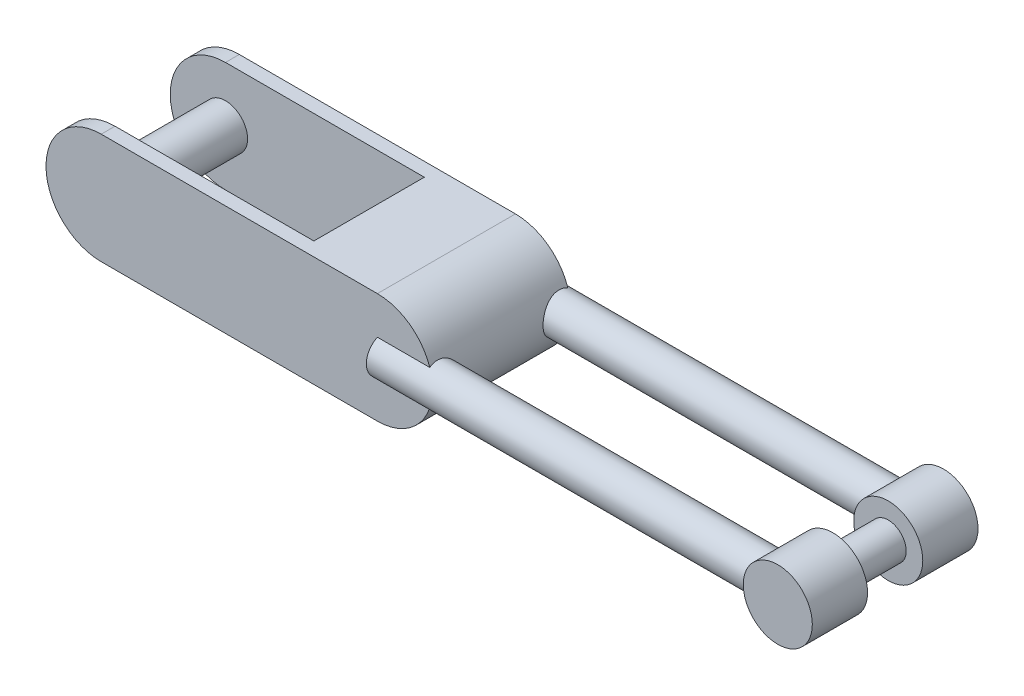
SolidWorks part; units mm, degrees
material "Brass"
ref_plane "Front Plane" through (0, 0, 0) normal (0, 0, 1) x (1, 0, 0)
ref_plane "Top Plane" through (0, 0, 0) normal (0, 1, 0) x (1, 0, 0)
ref_plane "Right Plane" through (0, 0, 0) normal (1, 0, 0) x (0, 0, -1)
other "Configuration Table"
sketch "Sketch1" plane through (0, 0, 0) normal (0, 0, 1) x (1, 0, 0)
  line L0 (0, 10) -> (50, 10)
  line L1 (0, -10) -> (50, -10)
  circle A0 centre (0, 0) radius 10
  circle A1 centre (50, 0) radius 10
  dimension "D1" = 20
  dimension "D2" = 20
  dimension "D3" = 50
extrude "Extrude1" add sketch "Sketch1" against normal mid plane 25
sketch "Sketch2" plane through (0, 10, 0) normal (0, 1, 0) x (-1, 0, 0)
  line L1 (-36, 10) -> (14, 10)
  line L2 (-36, 10) -> (-36, -10)
  line L3 (-36, -10) -> (14, -10)
  line L4 (14, 10) -> (14, -10)
  line L5 (-50, 0) -> (-36, 0) construction
  line L6 (-50, -12.5) -> (-50, 12.5) construction
  dimension "D1" = 20
  dimension "D2" = 50
  dimension "D3" = 14
extrude "Cut-Extrude1" cut sketch "Sketch2" against normal through all
ref_plane "Plane1" through (25, 10, 12.5) normal (1, 0, 0) x (0, 1, 0)
ref_plane "Plane2" through (50, 0, 0) normal (1, 0, 0) x (0, 1, 0)
sketch "Sketch3" plane through (50, 0, 0) normal (1, 0, 0) x (0, 1, 0)
  line L1 (10, 12.5) -> (-10, 12.5) construction
  circle A0 centre (0, 11) radius 3.5
  dimension "D1" = 7
  dimension "D3" = 10
  dimension "D2" = 1.5
extrude "Extrude2" add sketch "Sketch3" along normal blind 70
ref_plane "Plane3" through (0, 0, 0) normal (0, 0, 1) x (1, 0, 0)
mirror "Mirror1" about plane through (0, 0, 0) normal (0, 0, 1) of "Extrude2"
sketch "Sketch4" plane through (0, 0, 0) normal (0, 0, 1) x (1, 0, 0)
  circle A1 centre (125, 0) radius 6.25
  dimension "D2" = 12.5
  dimension "D3" = 75
extrude "Extrude3" add sketch "Sketch4" against normal mid plane 30
sketch "Sketch7" plane through (0, 0, 0) normal (0, 0, 1) x (1, 0, 0)
  circle A0 centre (125, 0) radius 6.25 construction
  circle A1 centre (125, 0) radius 6.25
  circle A2 centre (125, 0) radius 3.25
  dimension "D1" = 6.5
extrude "Extrude6" cut sketch "Sketch7" against normal mid plane 10
fillet "Fillet4" [suppressed] radius 0.5
ref_point "Point1"
ref_point "Point2"
sketch "Sketch6" plane through (0, 0, -10) normal (0, 0, 1) x (1, 0, 0)
  circle A0 centre (0, 0) radius 4
  dimension "D1" = 8
extrude "Extrude5" add sketch "Sketch6" along normal up to surface (20 mm away) up to face at (15.5, 0, 10)
